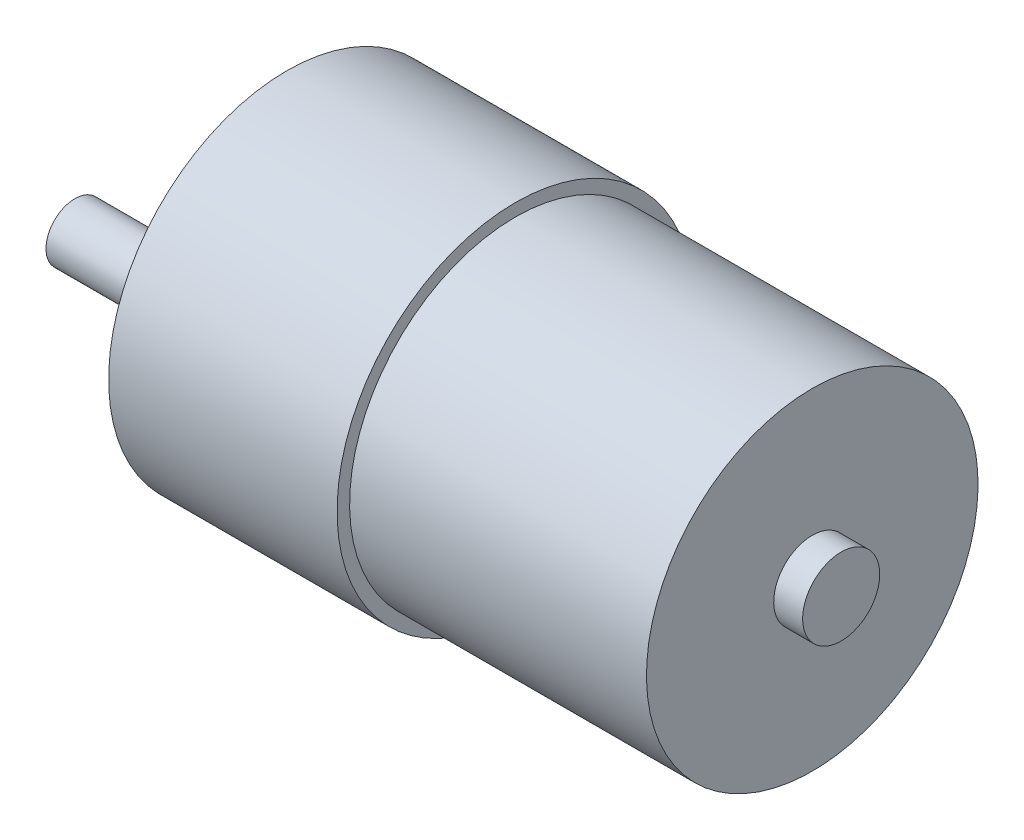
SolidWorks part; units mm, degrees
ref_plane "Front Plane" through (0, 0, 0) normal (0, 0, 1) x (1, 0, 0)
ref_plane "Top Plane" through (0, 0, 0) normal (0, 1, 0) x (1, 0, 0)
ref_plane "Right Plane" through (0, 0, 0) normal (1, 0, 0) x (0, 0, -1)
sketch "Sketch1" plane through (0, 0, 0) normal (0, 0, 1) x (1, 0, 0)
  line L0 (0, 17.2) -> (30.8, 17.2)
  line L1 (0, 0) -> (-23.7, 0)
  line L2 (0, 0) -> (0, 18.5)
  line L3 (0, 18.5) -> (-23.7, 18.5)
  line L4 (-23.7, 0) -> (-23.7, 18.5)
  line L5 (30.8, 17.2) -> (30.8, 0)
  line L6 (30.8, 0) -> (0, 0)
  line L7 (30.8, 4) -> (33.8, 4)
  line L8 (33.8, 4) -> (33.8, 0)
  line L9 (33.8, 0) -> (30.8, 0)
  dimension "D1" = 17.2
  dimension "D2" = 18.5
  dimension "D3" = 23.7
  dimension "D4" = 30.8
  dimension "D5" = 3
  dimension "D6" = 4
revolve "Revolve1" add sketch "Sketch1" angle 360 about L6
sketch "Sketch2" plane through (-23.7, 0, 0) normal (-1, 0, 0) x (0, 0, 1)
  circle A0 centre (0, -7) radius 6.5
  circle A1 centre (0, 0) radius 18.5 construction
  dimension "D1" = 7
  dimension "D2" = 13
extrude "Boss-Extrude1" add sketch "Sketch2" along normal blind 7
sketch "Sketch3" plane through (-30.7, 0, 0) normal (-1, 0, 0) x (0, 0, 1)
  circle A0 centre (0, -7) radius 3
  dimension "D1" = 6
extrude "Boss-Extrude2" add sketch "Sketch3" along normal blind 15
